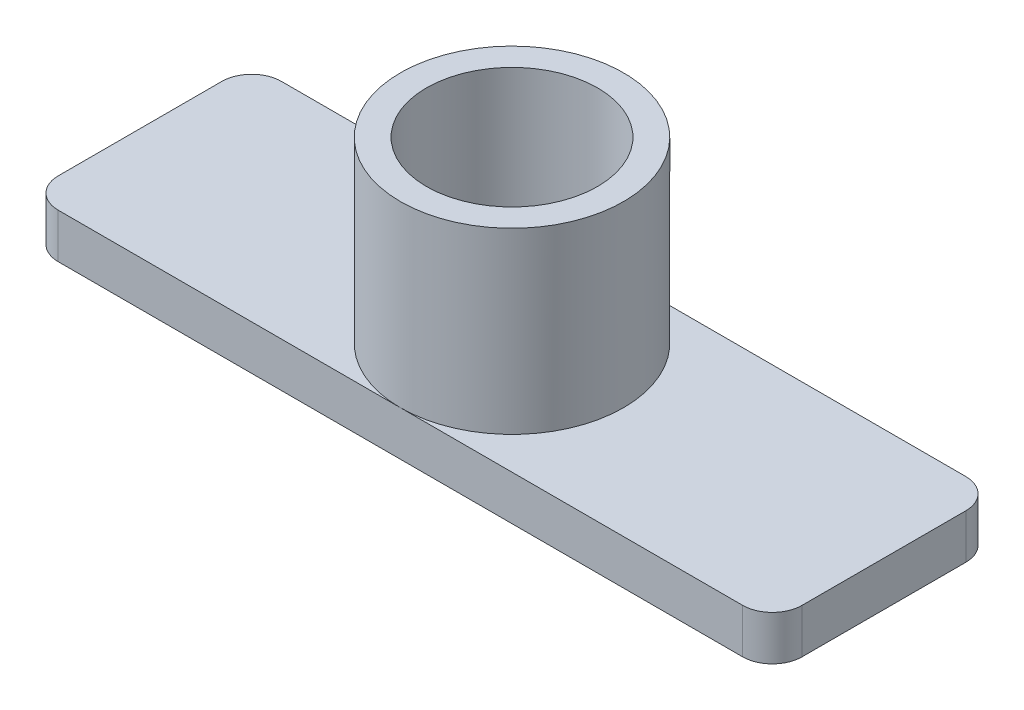
SolidWorks part; units mm, degrees
ref_plane "Ebene vorne" through (0, 0, 0) normal (0, 0, 1) x (1, 0, 0)
ref_plane "Ebene oben" through (0, 0, 0) normal (0, 1, 0) x (1, 0, 0)
ref_plane "Ebene rechts" through (0, 0, 0) normal (1, 0, 0) x (0, 0, -1)
sketch "Skizze1" plane through (0, 0, 0) normal (0, 1, 0) x (1, 0, 0)
  line L1 (-25, -7.5) -> (25, -7.5)
  line L2 (-25, -7.5) -> (-25, 7.5)
  line L3 (-25, 7.5) -> (25, 7.5)
  line L4 (25, -7.5) -> (25, 7.5)
  line L5 (-25, -7.5) -> (25, 7.5) construction
  line L6 (-25, 7.5) -> (25, -7.5) construction
  point P0 (0, 0)
  dimension "D1" = 50
  dimension "D2" = 15
extrude "Aufsatz-Linear austragen1" add sketch "Skizze1" along normal blind 3
sketch "Skizze2" plane through (0, 3, 0) normal (0, 1, 0) x (1, 0, 0)
  circle A0 centre (0, 0) radius 7.5
  circle A1 centre (0, 0) radius 5.75
  dimension "D1" = 15
  dimension "D2" = 11.5
extrude "Aufsatz-Linear austragen2" add sketch "Skizze2" along normal blind 12
fillet "Verrundung1" radius 2 4 edges at (25, 1.5, -7.5) (25, 1.5, 7.5) (-25, 1.5, 7.5) (-25, 1.5, -7.5)
